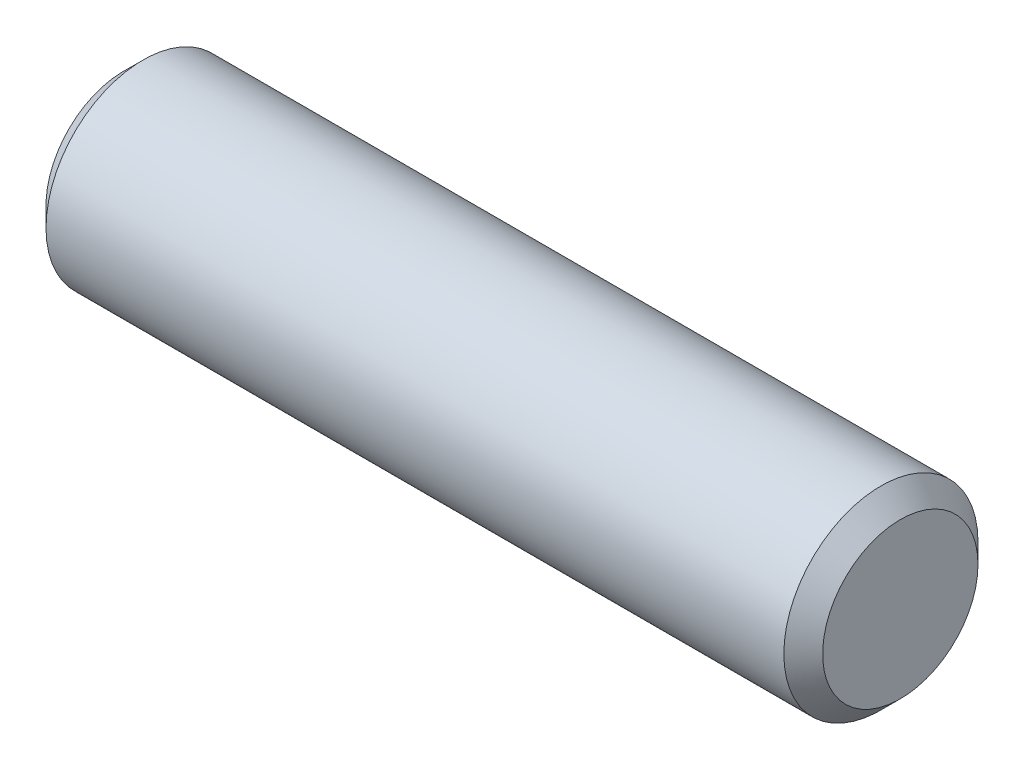
SolidWorks part; units mm, degrees
ref_plane "Front" through (0, 0, 0) normal (0, 0, 1) x (1, 0, 0)
ref_plane "Top" through (0, 0, 0) normal (0, 1, 0) x (1, 0, 0)
ref_plane "Right" through (0, 0, 0) normal (1, 0, 0) x (0, 0, -1)
sketch "Sketch1" plane through (0, 0, 0) normal (0, 0, 1) x (1, 0, 0)
  line L0 (-6.35, 0) -> (6.35, 0) construction
  line L1 (6.35, 1.5875) -> (6.35, -1.5875) construction
  line L2 (-6.35, 1.5875) -> (-6.35, -1.5875) construction
  dimension "Length" = 12.7
  dimension "Diameter" = 3.175
sketch "Sketch2" plane through (0, 0, 0) normal (1, 0, 0) x (0, 0, -1)
  circle A0 centre (0, 0) radius 1.5875
extrude "Extrude1" add sketch "Sketch2" against normal up to vertex (6.35 mm away) and the other way up to vertex (6.35 mm away) up to point (-6.35, 1.5875, 0) other way up to point (6.35, 1.5875, 0)
chamfer "Chamfer1" distance 0.3175 angle 45 2 edges at (6.35, 0, -1.5875) (-6.35, 0, -1.5875)
equation "\"D1@Chamfer1\" = \"Diameter@Sketch1\"*.1"
